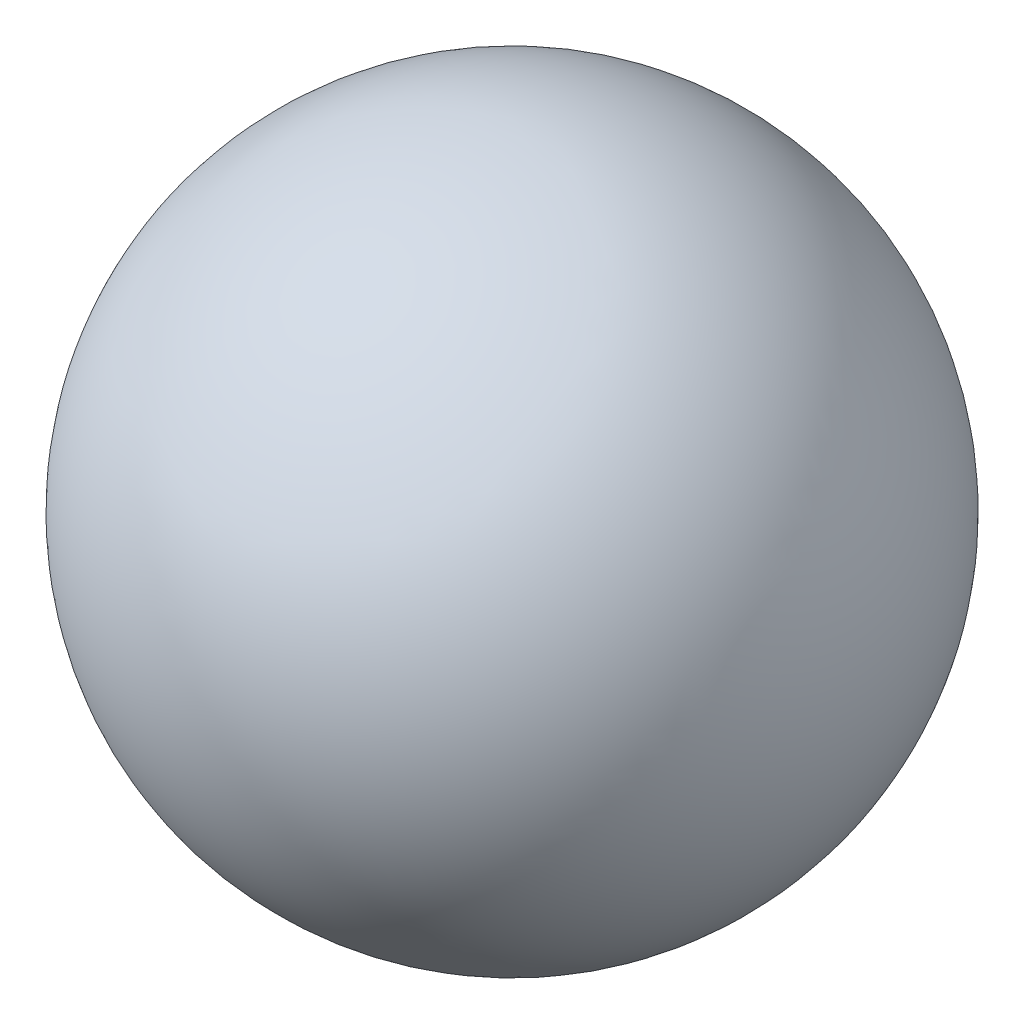
SolidWorks part; units mm, degrees
material "Chrome Stainless Steel"
ref_plane "Front Plane" through (0, 0, 0) normal (0, 0, 1) x (1, 0, 0)
ref_plane "Top Plane" through (0, 0, 0) normal (0, 1, 0) x (1, 0, 0)
ref_plane "Right Plane" through (0, 0, 0) normal (1, 0, 0) x (0, 0, -1)
sketch "RevolveS" plane through (0, 0, 0) normal (0, 0, 1) x (1, 0, 0)
  line L0 (1, 0) -> (-1, 0) construction
  line L1 (1, 0) -> (-1, 0)
  arc A0 (1, 0) -> (-1, 0) centre (0, 0) ccw
  dimension "Dia" = 2
revolve "Revolve" add sketch "RevolveS" angle 360 about L0
